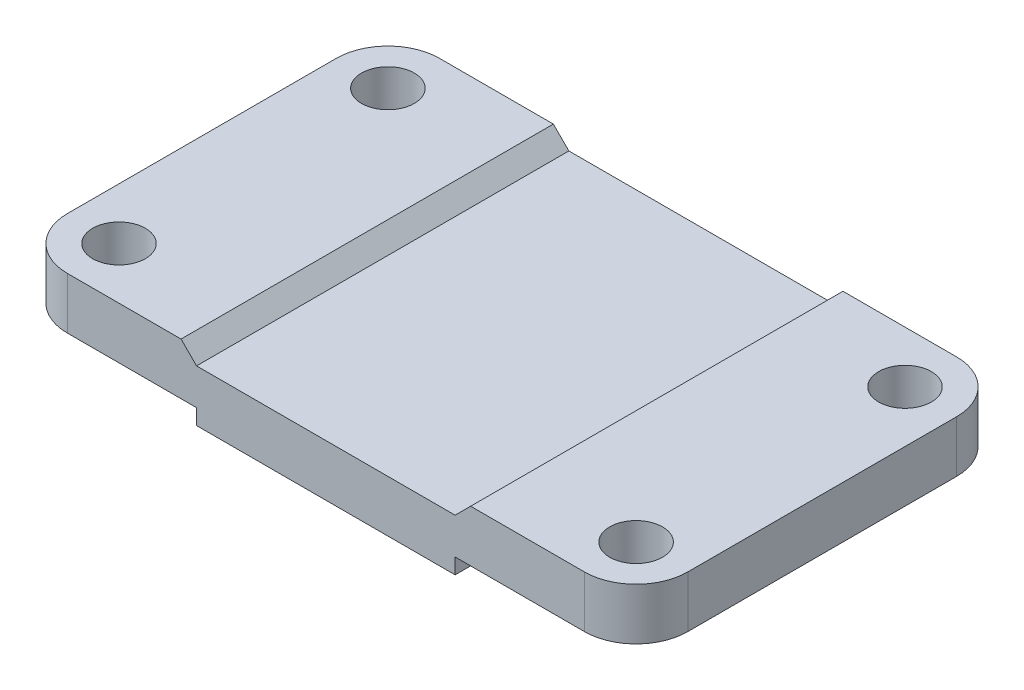
SolidWorks part; units mm, degrees
ref_plane "Front Plane" through (0, 0, 0) normal (0, 0, 1) x (1, 0, 0)
ref_plane "Top Plane" through (0, 0, 0) normal (0, 1, 0) x (1, 0, 0)
ref_plane "Right Plane" through (0, 0, 0) normal (1, 0, 0) x (0, 0, -1)
sketch "Sketch1" plane through (0, 0, 0) normal (0, 1, 0) x (1, 0, 0)
  line L1 (-60, 36) -> (60, 36)
  line L2 (-60, 36) -> (-60, -36)
  line L3 (-60, -36) -> (60, -36)
  line L4 (60, 36) -> (60, -36)
  line L5 (-60, 36) -> (60, -36) construction
  line L6 (-60, -36) -> (60, 36) construction
  point P0 (0, 0)
  dimension "D1" = 120
  dimension "D2" = 72
extrude "Boss-Extrude1" add sketch "Sketch1" along normal blind 10
fillet "Fillet1" radius 10 4 edges at (-60, 5, 36) (-60, 5, -36) (60, 5, -36) (60, 5, 36)
hole_wizard "M12 Tapped Hole1" positions "Sketch4" profile "Sketch5" tap size "M12" standard "GB" end condition up to next
sketch "Sketch4" plane through (0, 0, 0) normal (0, 1, 0) x (1, 0, 0)
  point P0 (50, 26)
  point P3 (50, -26)
  point P6 (-50, -26)
  point P9 (-50, 26)
sketch "Sketch5" plane through (50, 0, -26) normal (1, 0, 0) x (0, 0, -1)
  line L0 (0, 0) -> (0, 10)
  line L1 (0, 10) -> (5.1, 10)
  line L2 (5.1, 10) -> (5.1, 0)
  line L5 (5.1, 0) -> (0, 0)
  line L11 (0, -6.35) -> (0, 107.95) construction
  dimension "Thru Tap Drill Dia." = 10.2
  dimension "Thru Tap Drill Depth" = 10
cosmetic thread "Hole Thread1" parameters "D2"=12
cosmetic thread "Hole Thread2" parameters "D2"=12
cosmetic thread "Hole Thread3" parameters "D2"=12
cosmetic thread "Hole Thread4" parameters "D2"=12
sketch "Sketch6" plane through (0, 0, 0) normal (0, 1, 0) x (1, 0, 0)
  line L0 (-50, -36) -> (50, -36) construction
  line L1 (-25, 36) -> (25, 36)
  line L2 (-25, 36) -> (-25, -36)
  line L3 (-25, -36) -> (25, -36)
  line L4 (25, 36) -> (25, -36)
  line L5 (-25, 36) -> (25, -36) construction
  line L6 (-25, -36) -> (25, 36) construction
  point P0 (0, 0)
  dimension "D1" = 50
extrude "Boss-Extrude2" add sketch "Sketch6" against normal blind 3
sketch "Sketch11" plane through (0, 0, 36) normal (0, 0, 1) x (1, 0, 0)
  line L0 (-28, 10) -> (-25, 7)
  line L1 (50, 10) -> (-50, 10) construction
  line L2 (-25, 7) -> (25, 7)
  line L3 (25, 7) -> (28, 10)
  line L4 (28, 10) -> (-28, 10)
  line L5 (0, 10) -> (0, 6.7699) construction
  point P8 (0, 0)
  dimension "D1" = 45
  dimension "D2" = 50
  dimension "D3" = 56
extrude "Cut-Extrude1" cut sketch "Sketch11" against normal through all
